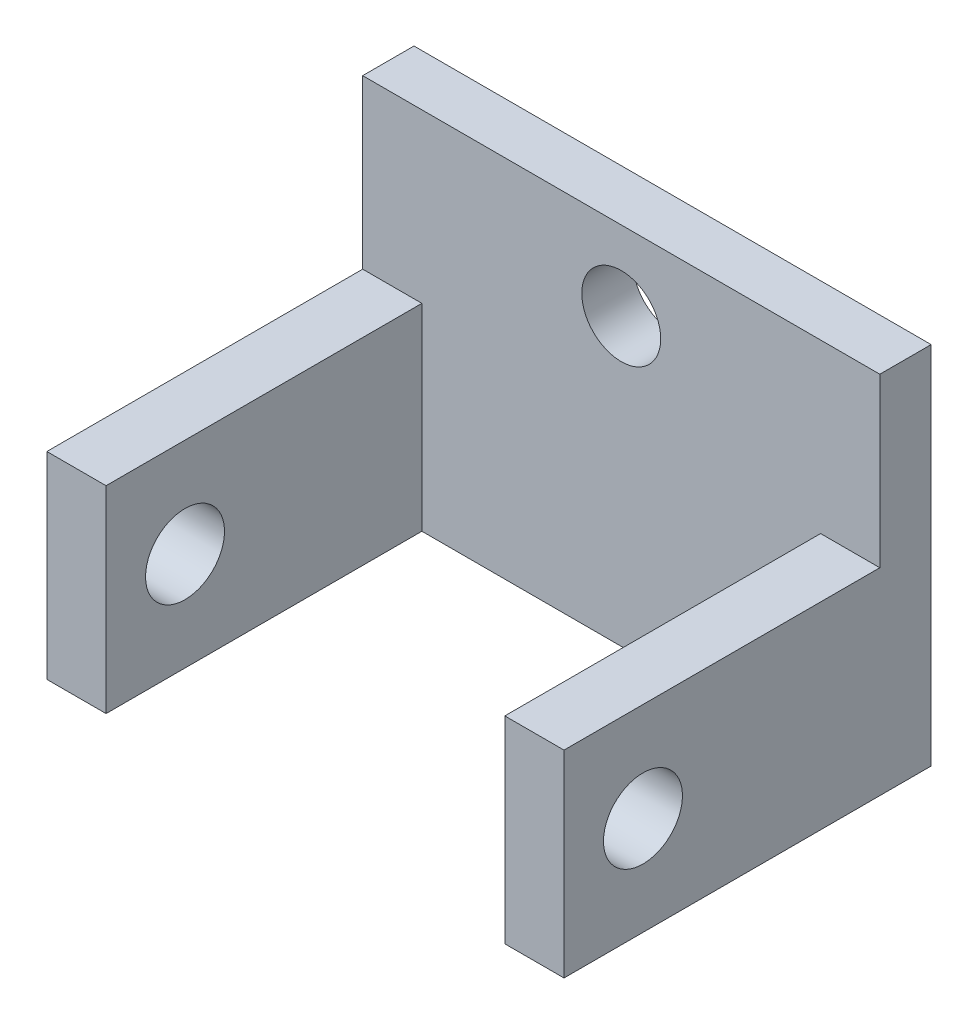
SolidWorks part; units mm, degrees
ref_plane "Front" through (0, 0, 0) normal (0, 0, 1) x (1, 0, 0)
ref_plane "Top" through (0, 0, 0) normal (0, 1, 0) x (1, 0, 0)
ref_plane "Right" through (0, 0, 0) normal (1, 0, 0) x (0, 0, -1)
sketch "草图1" plane through (0, 0, 0) normal (0, 0, 1) x (1, 0, 0)
  line L1 (0, 0) -> (13.1, 0)
  line L2 (0, 0) -> (0, 9.2456)
  line L3 (0, 9.2456) -> (13.1, 9.2456)
  line L4 (13.1, 0) -> (13.1, 9.2456)
  circle A0 centre (6.55, 7.2456) radius 1
  dimension "D1" = 2
  dimension "D2" = 6.55
extrude "凸台-拉伸1" add sketch "草图1" along normal blind 1.3
sketch "草图2" plane through (0, 0, 1.3) normal (0, 0, 1) x (1, 0, 0)
  line L0 (0, 0) -> (13.1, 0) construction
  line L1 (0, 5) -> (1.5, 5)
  line L2 (0, 5) -> (0, 0)
  line L3 (0, 0) -> (1.5, 0)
  line L4 (1.5, 5) -> (1.5, 0)
  line L6 (13.1, 5) -> (11.6, 5)
  line L7 (13.1, 5) -> (13.1, 0)
  line L8 (13.1, 0) -> (11.6, 0)
  line L9 (11.6, 5) -> (11.6, 0)
  point P4 (13.1, 0)
extrude "凸台-拉伸2" add sketch "草图2" along normal blind 8
sketch "草图4" plane through (0, 0, 0) normal (-1, 0, 0) x (0, 0, 1)
  line L0 (9.3, 5) -> (9.3, 0) construction
  circle A0 centre (7.3, 2.5) radius 1
  dimension "D1" = 2
extrude "切除-拉伸1" cut sketch "草图4" against normal blind 15
